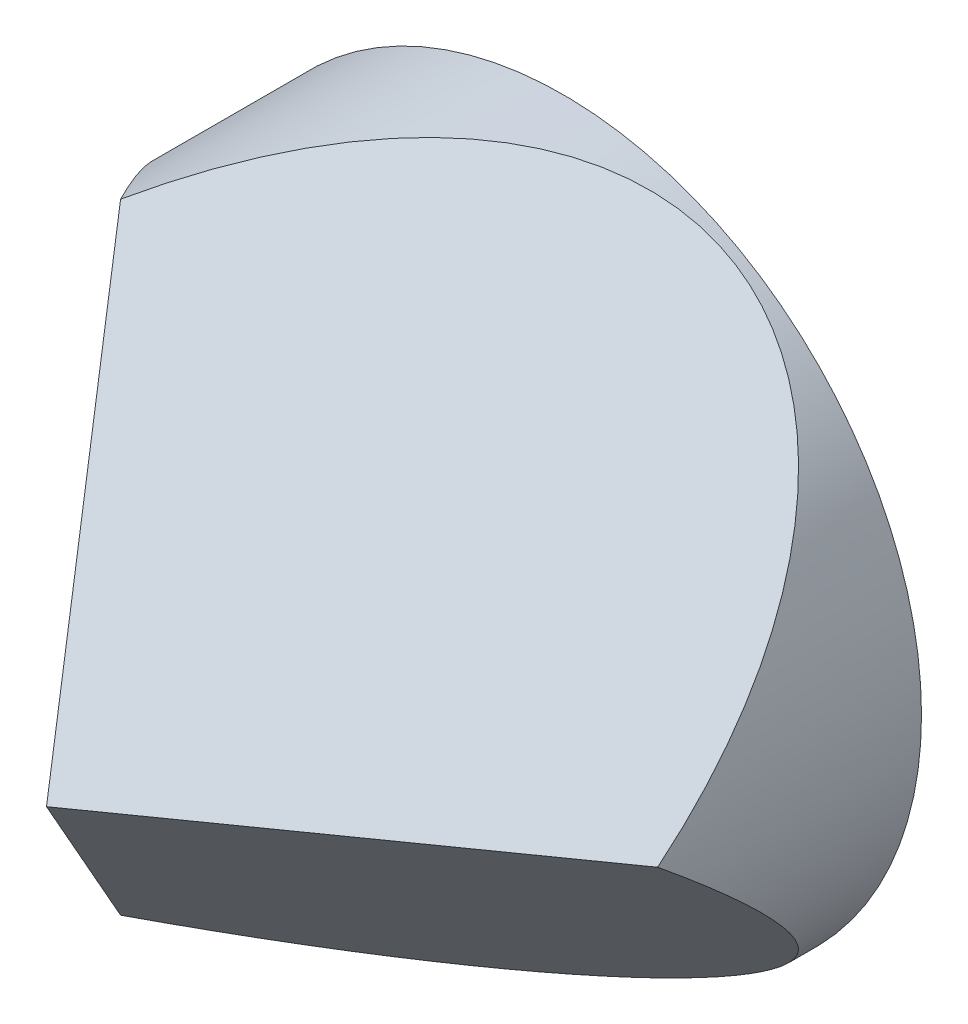
SolidWorks part; units mm, degrees
ref_plane "前视基准面" through (0, 0, 0) normal (0, 0, 1) x (1, 0, 0)
ref_plane "上视基准面" through (0, 0, 0) normal (0, 1, 0) x (1, 0, 0)
ref_plane "右视基准面" through (0, 0, 0) normal (1, 0, 0) x (0, 0, -1)
sketch "草图1" plane through (0, 0, 0) normal (0, 0, 1) x (1, 0, 0)
  circle A0 centre (0, 0) radius 36.25
  dimension "D1" = 72.5
extrude "凸台-拉伸1" add sketch "草图1" along normal blind 52.35
sketch "草图2" plane through (0, 0, 0) normal (0, 1, 0) x (1, 0, 0)
  line L0 (0, 0) -> (0, -52.35) construction
  line L1 (-36.25, -52.35) -> (36.25, -52.35) construction
  line L2 (0, -52.35) -> (-40.6903, 5.1829)
  line L3 (-40.6903, 5.1829) -> (-40.6903, -56.657)
  line L4 (-40.6903, -56.657) -> (0, -56.657)
  line L5 (0, -56.657) -> (0, -52.35)
  line L6 (36.25, 0) -> (-36.25, 0) construction
  dimension "D1" = 54.73
extrude "切除-拉伸1" cut sketch "草图2" against normal mid plane 79
sketch "草图3" plane through (0, 0, 52.35) normal (0, 0, 1) x (1, 0, 0)
  line L0 (0, 0) -> (16.7186, 0)
  line L1 (0, 0) -> (8.0189, 13.8892)
  line L2 (0, 0) -> (8.0629, -13.9654)
  dimension "D1" = 60
  dimension "D2" = 60
ref_plane "基准面1" through (0, 0, 0) normal (0.866, -0.5, 0) x (0.5, 0.866, 0)
ref_plane "基准面2" through (0, 0, 0) normal (-0.866, -0.5, 0) x (0.5, -0.866, 0)
sketch "草图4" plane through (0, 0, 0) normal (0.866, -0.5, 0) x (0.5, 0.866, 0)
  line L0 (0, 0) -> (0, 22.6417) construction
  line L2 (0, 52.35) -> (102.7972, -92.9971)
  line L3 (0, 52.35) -> (8.3593, 52.35) construction
  line L5 (102.7972, -92.9971) -> (102.7972, 79.0892)
  line L6 (102.7972, 79.0892) -> (0, 79.0892)
  line L7 (0, 79.0892) -> (0, 52.35)
  line L8 (-36.25, 0) -> (36.25, 0) construction
  dimension "D1" = 54.73
extrude "切除-拉伸2" cut sketch "草图4" along normal mid plane 124
sketch "草图5" plane through (0, 0, 0) normal (-0.866, -0.5, 0) x (0.5, -0.866, 0)
  line L0 (0, 52.35) -> (47.7882, -15.2187)
  line L1 (0, 52.35) -> (16.1259, 52.35) construction
  line L2 (47.7882, -15.2187) -> (47.7882, 62.0813)
  line L3 (47.7882, 62.0813) -> (2.6847, 62.0813)
  line L4 (2.6847, 62.0813) -> (0, 52.35)
  line L5 (-36.25, 0) -> (36.25, 0) construction
  dimension "D1" = 54.73
extrude "切除-拉伸3" cut sketch "草图5" against normal mid plane 107
